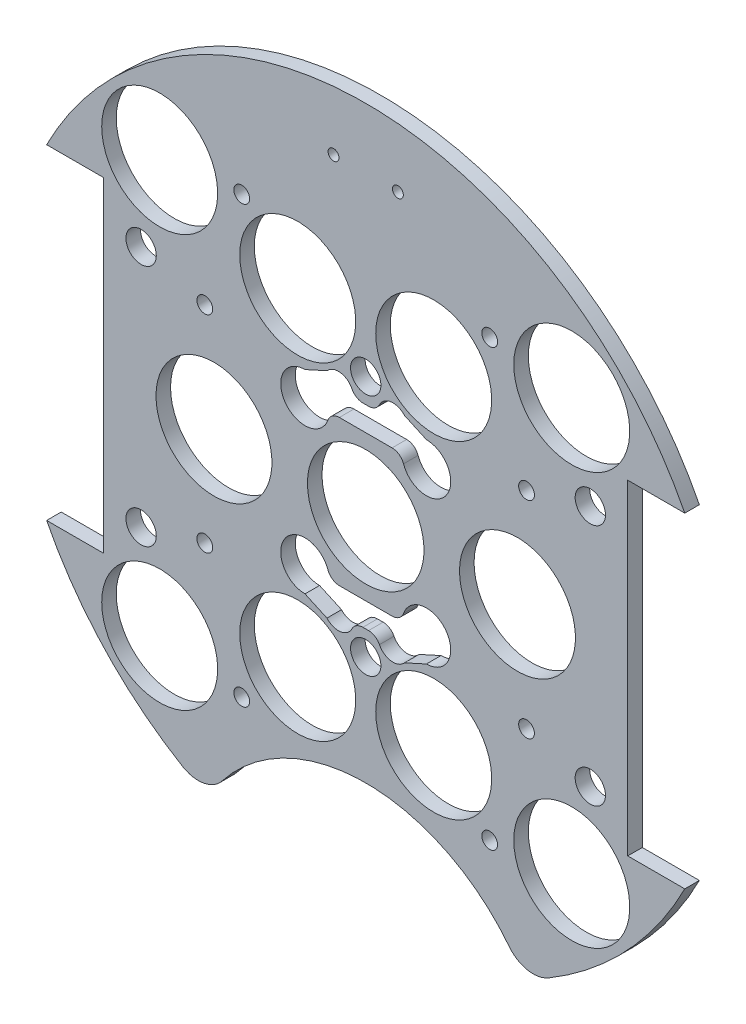
SolidWorks part; units mm, degrees
ref_plane "Front Plane" through (0, 0, 0) normal (0, 0, 1) x (1, 0, 0)
ref_plane "Top Plane" through (0, 0, 0) normal (0, 1, 0) x (1, 0, 0)
ref_plane "Right Plane" through (0, 0, 0) normal (1, 0, 0) x (0, 0, -1)
sketch "Sketch1" plane through (0, 0, 0) normal (0, 0, 1) x (1, 0, 0)
  line L0 (0, 0) -> (-82.1241, 0) construction
  line L1 (0, 0) -> (0, 95.6219) construction
  line L2 (0, -97.5637) -> (0, 139.5774) construction
  line L3 (-66.7537, 34.036) -> (-54.8157, 34.036)
  line L5 (-66.7537, -34.036) -> (-54.8157, -34.036)
  line L6 (-54.8157, 34.036) -> (-54.8157, -34.036)
  line L7 (66.7537, -34.036) -> (54.8157, -34.036)
  line L8 (66.7537, 34.036) -> (54.8157, 34.036)
  line L9 (54.8157, 34.036) -> (54.8157, -34.036)
  arc A0 (-66.7537, -34.036) -> (66.7537, -34.036) centre (0, 0) ccw
  arc A9 (66.7537, 34.036) -> (-66.7537, 34.036) centre (0, 0) ccw
  dimension "D6" = 68.072
  dimension "D7" = 11.938
  dimension "D8" = 74.93
  dimension "D9" = 74.93
  dimension "D11" = 34.036
extrude "Boss-Extrude2" add sketch "Sketch1" along normal blind 3.048
sketch "Sketch2" plane through (0, 0, 3.048) normal (0, 0, 1) x (1, 0, 0)
  line L0 (0, 95.0162) -> (0, -6.5218) construction
  circle A3 centre (-6.731, 62.23) radius 1.143
  circle A4 centre (6.731, 62.23) radius 1.143
  dimension "D4" = 2.286
  dimension "D1" = 62.23
  dimension "D2" = 13.462
extrude "Cut-Extrude1" cut sketch "Sketch2" against normal through all contours A3 | A4
sketch "Sketch4" plane through (0, 0, 0) normal (0, 0, -1) x (-1, 0, 0)
  line L0 (33.02, -67.2621) -> (-33.02, -67.2621)
  line L1 (0, 0) -> (0, -124.2152) construction
  arc A2 (-66.7537, -34.036) -> (66.7537, -34.036) centre (0, 0) ccw construction
  circle A3 centre (0, -86.3121) radius 38.1
  point P2 (0, -67.2621)
  dimension "D4" = 76.2
  dimension "D1" = 66.04
  dimension "D2" = 74.93
  dimension "D3" = 0
  dimension "D5" = 19.05
extrude "Cut-Extrude3" cut sketch "Sketch4" against normal blind 124.46 contours A3
extrude "Cut-Extrude5" cut sketch "Sketch6" against normal through all
sketch "Sketch6" plane through (31.3134, 132.559, 0) normal (0, 0, -1) x (0, 1, 0)
  line L0 (-132.559, -31.3134) -> (-245.9178, -31.3134) construction
  line L1 (-132.559, -31.3134) -> (-132.559, -129.4011) construction
  circle A0 centre (-180.819, -4.6434) radius 1.651
  circle A3 centre (-180.819, -57.9834) radius 1.651
  circle A4 centre (-84.299, -57.9834) radius 1.651
  circle A5 centre (-84.299, -4.6434) radius 1.651
extrude "Cut-Extrude6" cut sketch "Sketch7" against normal through all both and the other way through all
sketch "Sketch7" plane through (31.3134, 132.614, -31.75) normal (0, 0, -1) x (0, 1, 0)
  line L0 (-132.614, -31.3134) -> (-132.614, 57.8454) construction
  line L1 (-132.614, -31.3134) -> (-222.516, -31.3134) construction
  circle A0 centre (-158.014, 14.4066) radius 3.175
  circle A1 centre (-173.254, -31.3134) radius 3.175
  circle A3 centre (-158.014, -77.0334) radius 3.175
  circle A4 centre (-107.214, -77.0334) radius 3.175
  circle A5 centre (-91.974, -31.3134) radius 3.175
  circle A6 centre (-107.214, 14.4066) radius 3.175
fillet "Fillet1" radius 6.35 2 edges at (33.001, -67.2714, 1.524) (-33.001, -67.2714, 1.524)
extrude "Cut-Extrude7" cut sketch "Sketch8" against normal blind 29.21
sketch "Sketch8" plane through (31.3134, 132.559, -28.575) normal (0, 0, -1) x (0, 1, 0)
  line L0 (-132.559, -31.3134) -> (6.1626, -31.3134) construction
  line L2 (-132.559, -31.3134) -> (-132.559, -122.6589) construction
  circle A0 centre (-190.979, 2.9766) radius 1.651
  circle A2 centre (-154.784, -31.3134) radius 1.651
  circle A3 centre (-190.979, -65.6034) radius 1.651
  circle A4 centre (-110.334, -31.3134) radius 1.651
  circle A5 centre (-74.139, -65.6034) radius 1.651
  circle A6 centre (-74.139, 2.9766) radius 1.651
sketch "Sketch9" [suppressed] plane through (0, 0, 0) normal (0, 0, -1) x (-1, 0, 0)
  circle A0 centre (34.29, 58.42) radius 3.5
  circle A1 centre (-34.29, 58.42) radius 3.5
  circle A4 centre (-34.29, -58.42) radius 3.5
  circle A6 centre (34.29, -58.42) radius 3.5
  dimension "D1" = 7
  dimension "D2" = 7
  dimension "D5" = 7
  dimension "D6" = 7
extrude "Cut-Extrude8" [suppressed] cut sketch "Sketch9" against normal through all
extrude "Cut-Extrude11" cut sketch "Sketch12" against normal blind 75.692
sketch "Sketch12" plane through (30.092, 4.0835, 0) normal (0, 0, -1) x (-1, 0, 0)
  circle A0 centre (63.7572, 17.5065) radius 1.651
  circle A1 centre (63.7572, -25.6735) radius 1.651
  circle A2 centre (-3.5528, -25.6735) radius 1.651
  circle A3 centre (-3.5528, 17.5065) radius 1.651
extrude "Cut-Extrude13" cut sketch "Sketch14" against normal blind 97.79
sketch "Sketch14" plane through (30.092, 4.0835, -30.0355) normal (0, 0, -1) x (-1, 0, 0)
  line L0 (30.092, -29.4835) -> (30.092, 6.2385) construction
  circle A0 centre (4.1544, -49.7288) radius 1.651
  circle A4 centre (56.0296, -49.7288) radius 1.651
  circle A5 centre (4.1544, 41.3825) radius 1.651
  circle A9 centre (56.0296, 41.3825) radius 1.651
extrude "Cut-Extrude14" cut sketch "Sketch15" against normal blind 48.768 and the other way blind 103.378
sketch "Sketch15" plane through (30.092, 4.0835, 6.096) normal (0, 0, -1) x (-1, 0, 0)
  line L0 (30.092, -4.0835) -> (148.6336, -4.0835) construction
  line L1 (30.092, -4.0835) -> (30.092, 90.452) construction
  circle A0 centre (-16.898, 21.3165) radius 3.175
  circle A1 centre (77.082, 21.3165) radius 3.175
  circle A2 centre (30.092, 21.3165) radius 3.175
  circle A4 centre (77.082, -29.4835) radius 3.175
  circle A5 centre (30.092, -29.4835) radius 3.175
  circle A6 centre (-16.898, -29.4835) radius 3.175
sketch "Sketch3" plane through (0, 0, 0) normal (0, 0, -1) x (-1, 0, 0)
  line L0 (0, 0) -> (0, -15.4205) construction
  line L1 (0, 0) -> (-153.8039, 0) construction
  line L2 (0, 0) -> (4.0104, -14.967) construction
  line L5 (6.2818, -23.444) -> (15.2681, -56.9814) construction
  line L6 (0, -20.32) -> (0, -116.2908) construction
  line L7 (7.62, 15.24) -> (-7.62, 15.24)
  line L8 (7.62, -15.24) -> (-7.62, -15.24)
  line L9 (-12.7, -15.24) -> (12.7, 15.24) construction
  line L10 (-12.7, 15.24) -> (12.7, -15.24) construction
  line L12 (2.54, -20.32) -> (-2.54, -20.32)
  line L14 (2.54, 20.32) -> (-2.54, 20.32)
  line L15 (12.7, 20.32) -> (8.1071, 22.4077)
  line L16 (-8.1071, 22.4077) -> (-12.7, 20.32)
  line L17 (12.7, -20.32) -> (8.1071, -22.4077)
  line L18 (-8.1071, -22.4077) -> (-12.7, -20.32)
  circle A0 centre (-31.75, 0) radius 12.1285
  circle A1 centre (31.75, 0) radius 12.1285
  arc A2 (38.2787, -64.4146) -> (66.7537, -34.036) centre (0, 0) ccw construction
  circle A3 centre (0, 0) radius 12.192
  circle A4 centre (-43.1052, -43.1052) radius 12.1285
  arc A5 (8.1071, 22.4077) -> (2.54, 20.32) centre (5.715, 20.32) ccw
  circle A6 centre (14.224, -34.29) radius 12.1285
  circle A7 centre (14.224, 34.29) radius 12.1285
  circle A8 centre (-43.1052, 43.1052) radius 12.1285
  arc A9 (-2.54, 20.32) -> (-8.1071, 22.4077) centre (-5.715, 20.32) ccw
  arc A10 (-2.54, -20.32) -> (-8.1071, -22.4077) centre (-5.715, -20.32) cw
  circle A11 centre (43.1052, 43.1052) radius 12.1285
  circle A12 centre (-14.224, 34.29) radius 12.1285
  circle A13 centre (-14.224, -34.29) radius 12.1285
  circle A14 centre (43.1052, -43.1052) radius 12.1285
  arc A15 (8.1071, -22.4077) -> (2.54, -20.32) centre (5.715, -20.32) cw
  arc A16 (12.7, -20.32) -> (7.62, -15.24) centre (12.7, -15.24) ccw
  arc A17 (-7.62, -15.24) -> (-12.7, -20.32) centre (-12.7, -15.24) ccw
  arc A18 (7.62, 15.24) -> (12.7, 20.32) centre (12.7, 15.24) ccw
  arc A19 (-12.7, 20.32) -> (-7.62, 15.24) centre (-12.7, 15.24) ccw
  point P36 (0, 0)
  point P53 (0, 0)
  point P55 (0, 0)
  dimension "D1" = 63.5
  dimension "D2" = 25.4
  dimension "D3" = 30.48
  dimension "D4" = 15
  dimension "D5" = 14.224
  dimension "D6" = 34.29
  dimension "D7" = 43.1052
  dimension "D8" = 24.257
  dimension "D9" = 43.1052
  dimension "D10" = 24.384
  dimension "D11" = 6.35
  dimension "D12" = 6.35
  dimension "D13" = 11.43
  dimension "D14" = 20.32
  dimension "D15" = 5.715
extrude "Cut-Extrude2" cut sketch "Sketch3" against normal through all
fillet "Fillet2" radius 2.54 8 edges at (2.54, 20.32, 1.524) (-2.54, 20.32, 1.524) (-7.62, 15.24, 1.524) (7.62, 15.24, 1.524) (7.62, -15.24, 1.524) (-7.62, -15.24, 1.524) (-2.54, -20.32, 1.524) (2.54, -20.32, 1.524)
